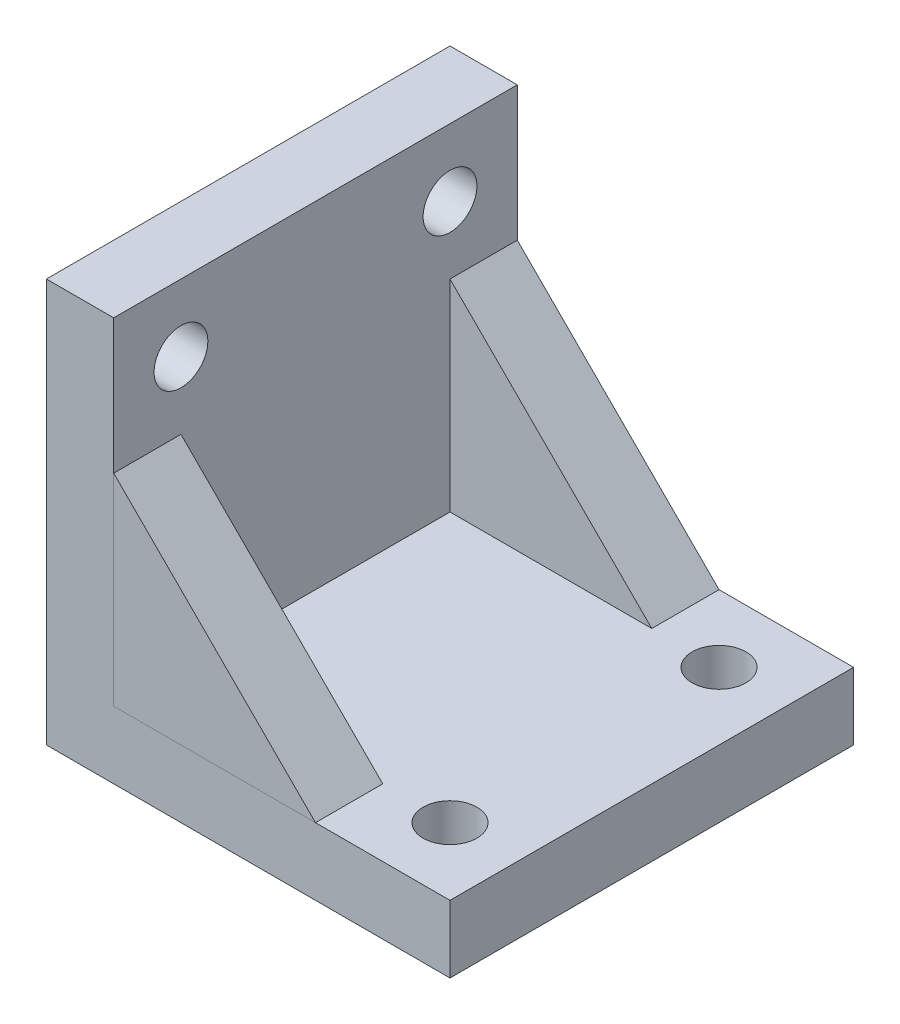
SolidWorks part; units mm, degrees
material "ABS"
ref_plane "Front Plane" through (0, 0, 0) normal (0, 0, 1) x (1, 0, 0)
ref_plane "Top Plane" through (0, 0, 0) normal (0, 1, 0) x (1, 0, 0)
ref_plane "Right Plane" through (0, 0, 0) normal (1, 0, 0) x (0, 0, -1)
sketch "Sketch1" plane through (0, 0, 0) normal (0, 1, 0) x (1, 0, 0)
  line L1 (-15, -15) -> (15, -15)
  line L2 (-15, -15) -> (-15, 15)
  line L3 (-15, 15) -> (15, 15)
  line L4 (15, -15) -> (15, 15)
  line L5 (-15, -15) -> (15, 15) construction
  line L6 (-15, 15) -> (15, -15) construction
  point P0 (0, 0)
  dimension "D1" = 30
  dimension "D2" = 30
extrude "Boss-Extrude1" add sketch "Sketch1" along normal blind 5
sketch "Sketch2" plane through (0, 5, 0) normal (0, 1, 0) x (1, 0, 0)
  line L0 (-15, -15) -> (15, -15) construction
  line L1 (-15, 15) -> (-10, 15)
  line L2 (-15, 15) -> (-15, -15)
  line L3 (-15, -15) -> (-10, -15)
  line L4 (-10, 15) -> (-10, -15)
  dimension "D1" = 5
extrude "Boss-Extrude2" add sketch "Sketch2" along normal blind 25
ref_plane "Plane1" through (0, 0, 15) normal (0, 0, 1) x (1, 0, 0)
sketch "Sketch3" plane through (0, 0, 15) normal (0, 0, 1) x (1, 0, 0)
  line L0 (-10, 5) -> (-10, 20)
  line L1 (-10, 30) -> (-10, 5) construction
  line L2 (-10, 20) -> (5, 5)
  line L3 (-10, 5) -> (15, 5) construction
  line L4 (5, 5) -> (-10, 5)
  dimension "D1" = 15
  dimension "D2" = 15
extrude "Boss-Extrude3" add sketch "Sketch3" against normal blind 5 separate body
ref_plane "Plane2" through (0, 0, -15) normal (0, 0, 1) x (1, 0, 0)
sketch "Sketch5" plane through (0, 0, -15) normal (0, 0, 1) x (1, 0, 0)
  line L0 (-10, 5) -> (-10, 20)
  line L1 (-10, 30) -> (-10, 5) construction
  line L2 (5, 5) -> (-10, 20) construction
  line L3 (-10, 20) -> (5, 5)
  line L4 (15, 5) -> (-10, 5) construction
  line L5 (5, 5) -> (-10, 5)
  dimension "D1" = 15
extrude "Boss-Extrude4" add sketch "Sketch5" along normal blind 5
sketch "Sketch10" plane through (-10, 0, 0) normal (1, 0, 0) x (0, 0, -1)
  line L0 (-15, 30) -> (-15, 5) construction
  line L1 (-15, 30) -> (15, 30) construction
  line L2 (15, 30) -> (15, 20) construction
  circle A0 centre (-10, 25) radius 2
  circle A1 centre (10, 25) radius 2
  dimension "D1" = 4
  dimension "D4" = 4
  dimension "D2" = 5
  dimension "D3" = 5
  dimension "D5" = 5
  dimension "D6" = 5
extrude "Cut-Extrude1" cut sketch "Sketch10" against normal blind 5
sketch "Sketch11" plane through (0, 5, 0) normal (0, 1, 0) x (1, 0, 0)
  line L0 (15, -15) -> (15, 15) construction
  line L1 (15, 15) -> (5, 15) construction
  line L2 (-10, -15) -> (15, -15) construction
  circle A0 centre (10, 10) radius 2
  circle A1 centre (10, -10) radius 2
  dimension "D1" = 4
  dimension "D4" = 4
  dimension "D2" = 5
  dimension "D3" = 5
  dimension "D5" = 5
  dimension "D6" = 5
extrude "Cut-Extrude2" cut sketch "Sketch11" against normal blind 5
